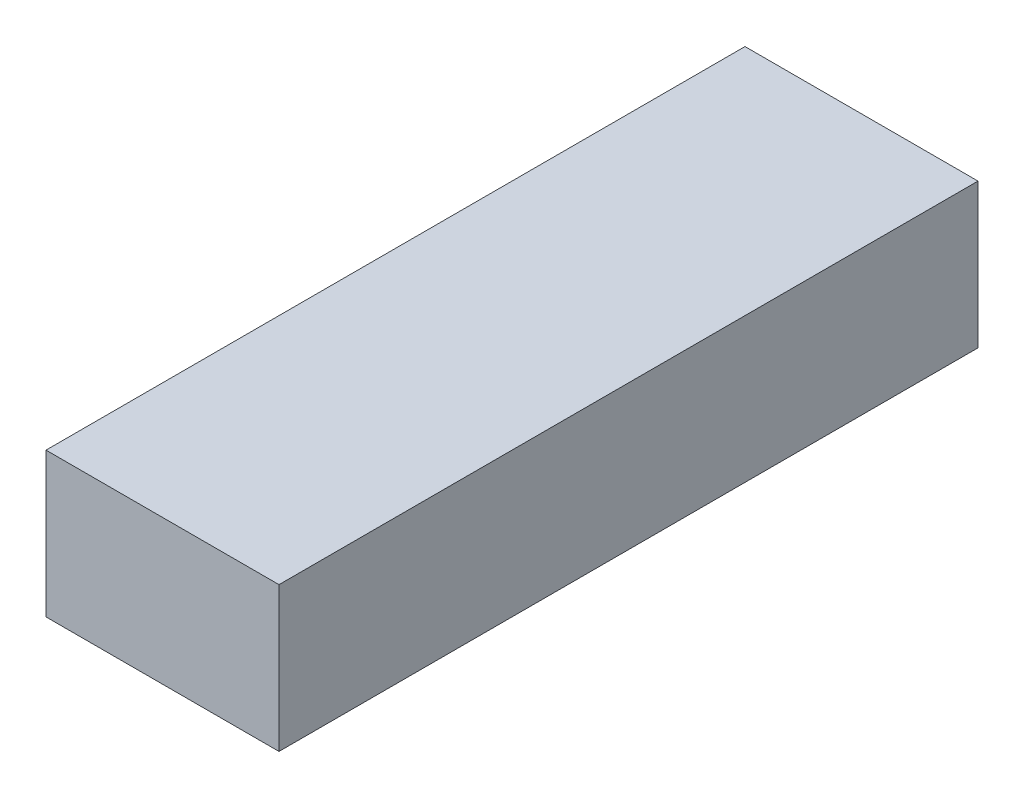
SolidWorks part; units mm, degrees
ref_plane "Front Plane" through (0, 0, 0) normal (0, 0, 1) x (1, 0, 0)
ref_plane "Top Plane" through (0, 0, 0) normal (0, 1, 0) x (1, 0, 0)
ref_plane "Right Plane" through (0, 0, 0) normal (1, 0, 0) x (0, 0, -1)
sketch "Sketch3" plane through (0, 0, 0) normal (0, 1, 0) x (1, 0, 0)
  line L1 (-17.5, 0) -> (17.5, 0)
  line L2 (-17.5, 0) -> (-17.5, 105)
  line L3 (-17.5, 105) -> (17.5, 105)
  line L4 (17.5, 0) -> (17.5, 105)
  point P5 (0, 0)
  dimension "D1" = 105
  dimension "D2" = 35
extrude "Boss-Extrude1" add sketch "Sketch3" along normal blind 21.7
